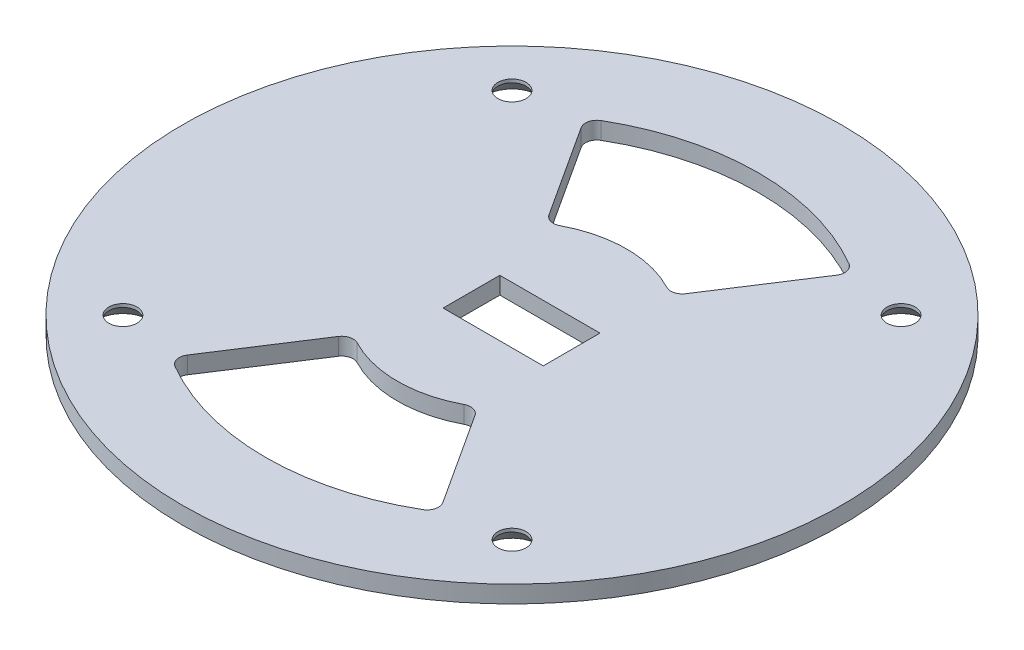
SolidWorks part; units mm, degrees
material "ABS"
ref_plane "Front Plane" through (0, 0, 0) normal (0, 0, 1) x (1, 0, 0)
ref_plane "Top Plane" through (0, 0, 0) normal (0, 1, 0) x (1, 0, 0)
ref_plane "Right Plane" through (0, 0, 0) normal (1, 0, 0) x (0, 0, -1)
sketch "Sketch1" plane through (0, 0, 0) normal (0, 1, 0) x (1, 0, 0)
  line L0 (0, 57.5) -> (0, 0) construction
  line L1 (0, 0) -> (-57.5, 0) construction
  line L2 (-57.5, 0) -> (-40.6586, 40.6586) construction
  line L3 (-40.6586, 40.6586) -> (0, 57.5) construction
  line L4 (-40.6586, 40.6586) -> (0, 0) construction
  line L5 (-3, 4.95) -> (6.325, 4.95)
  line L7 (-3, 4.95) -> (-3, -4.95)
  line L8 (-3, -4.95) -> (6.325, -4.95)
  line L9 (6.325, 4.95) -> (6.325, -4.95)
  line L14 (-3, -4.95) -> (6.325, -4.95) construction
  circle A0 centre (0, 0) radius 57.5
  circle A1 centre (-33.9411, 33.9411) radius 0.5
  circle A2 centre (33.9411, 33.9411) radius 0.5
  circle A3 centre (33.9411, -33.9411) radius 0.5
  circle A4 centre (-33.9411, -33.9411) radius 0.5
  point P17 (0, 0)
  dimension "D2" = 115
  dimension "D3" = 1
  dimension "D1" = 48
  dimension "D5" = 9.9
  dimension "D7" = 9.325
  dimension "D6" = 3
  dimension "D4" = 4
extrude "Boss-Extrude1" add sketch "Sketch1" along normal blind 3
hole_wizard "CSK for #8 Flat Head Socket Cap Screw1" positions "Sketch3" profile "Sketch2" countersink size "#8" standard "ANSI Inch" end condition through all
sketch "Sketch3" plane through (0, 0, 0) normal (0, -1, 0) x (-1, 0, 0)
  point P0 (33.9411, -33.9411)
  point P3 (-33.9411, -33.9411)
  point P6 (-33.9411, 33.9411)
  point P9 (33.9411, 33.9411)
sketch "Sketch2" plane through (-33.9411, 0, 33.9411) normal (1, 0, 0) x (0, 0, -1)
  line L0 (0, 0) -> (0, 3)
  line L1 (0, 3) -> (2.4574, 3)
  line L2 (2.4574, 3) -> (2.4574, 2.4179)
  line L3 (2.4574, 2.4179) -> (4.5593, 0)
  line L5 (4.5593, 0) -> (0, 0)
  line L6 (-2.4575, 2.4179) -> (-4.5593, 0) construction
  line L11 (0, -6.35) -> (0, 107.95) construction
  dimension "Thru Hole Dia." = 4.9149
  dimension "Thru Hole Depth" = 3
  dimension "Near C'Sink Dia." = 9.1186
  dimension "Near C'Sink Angle" = 82
sketch "Sketch5" plane through (0, 0, 0) normal (0, -1, 0) x (1, 0, 0)
  line L0 (1.6625, -4.95) -> (1.6625, 4.95) construction
  line L1 (6.325, -4.95) -> (10.4, -4.95)
  line L2 (6.325, -4.95) -> (6.325, 4.95)
  line L3 (6.325, 4.95) -> (10.4, 4.95)
  line L4 (10.4, -4.95) -> (10.4, 4.95)
  line L5 (6.325, -4.95) -> (-3, -4.95) construction
  line L6 (-3, 4.95) -> (6.325, 4.95) construction
  line L7 (-7.075, -4.95) -> (-7.075, 4.95)
  line L8 (-3, 4.95) -> (-7.075, 4.95)
  line L9 (-3, -4.95) -> (-3, 4.95)
  line L10 (-3, -4.95) -> (-7.075, -4.95)
  dimension "D1" = 4.075
extrude "Cut-Extrude2" cut sketch "Sketch5" against normal through all
sketch "Sketch10" plane through (0, 0, 0) normal (0, -1, 0) x (1, 0, 0)
  line L0 (0, 57.5) -> (0, 0) construction
  line L1 (0, 0) -> (57.5, 0) construction
  line L2 (23.4039, 36.0729) -> (10.8855, 16.7781)
  line L3 (-23.4039, 36.0729) -> (-10.8855, 16.7781)
  line L4 (0, 0) -> (10.8855, 16.7781) construction
  line L5 (0, 0) -> (-10.8855, 16.7781) construction
  line L6 (-23.4039, -36.0729) -> (-10.8855, -16.7781)
  line L7 (23.4039, -36.0729) -> (10.8855, -16.7781)
  circle A0 centre (0, 0) radius 57.5 construction
  arc A1 (23.4039, 36.0729) -> (-23.4039, 36.0729) centre (0, 0) ccw
  arc A2 (33.9411, 33.9411) -> (-34.0273, 33.8547) centre (0, 0) ccw construction
  arc A3 (10.8855, 16.7781) -> (-10.8855, 16.7781) centre (0, 0) ccw
  arc A4 (10.8855, -16.7781) -> (-10.8855, -16.7781) centre (0, 0) cw
  arc A5 (23.4039, -36.0729) -> (-23.4039, -36.0729) centre (0, 0) cw
  dimension "D1" = 5
  dimension "D2" = 20
  dimension "D3" = 10
extrude "Cut-Extrude4" cut sketch "Sketch10" against normal through all
fillet "Fillet3" radius 2 8 edges at (23.4039, 1.5, -36.0729) (-23.4039, 1.5, -36.0729) (10.8855, 1.5, -16.7781) (-10.8855, 1.5, -16.7781) (-23.4039, 1.5, 36.0729) (-10.8855, 1.5, 16.7781) (10.8855, 1.5, 16.7781) (23.4039, 1.5, 36.0729)
equation "\"D6@Sketch1\"=\"width keep@values@params_print.sldprt\""
equation "\"D7@Sketch1\"=\"pin diameter@values@params_print.sldprt\"+2*\"width keep@values@params_print.sldprt\"+\"print fit@values@params_print.sldprt\""
equation "\"D5@Sketch1\"=9.75 +\"print fit@values@params_print.sldprt\""
equation "\"D1@Boss-Extrude1\"=\"width keep@values@params_print.sldprt\""
equation "\"D1@Sketch5\" = \"width tab@values@params_print.sldprt\" + \"print fit@values@params_print.sldprt\" / 2"
